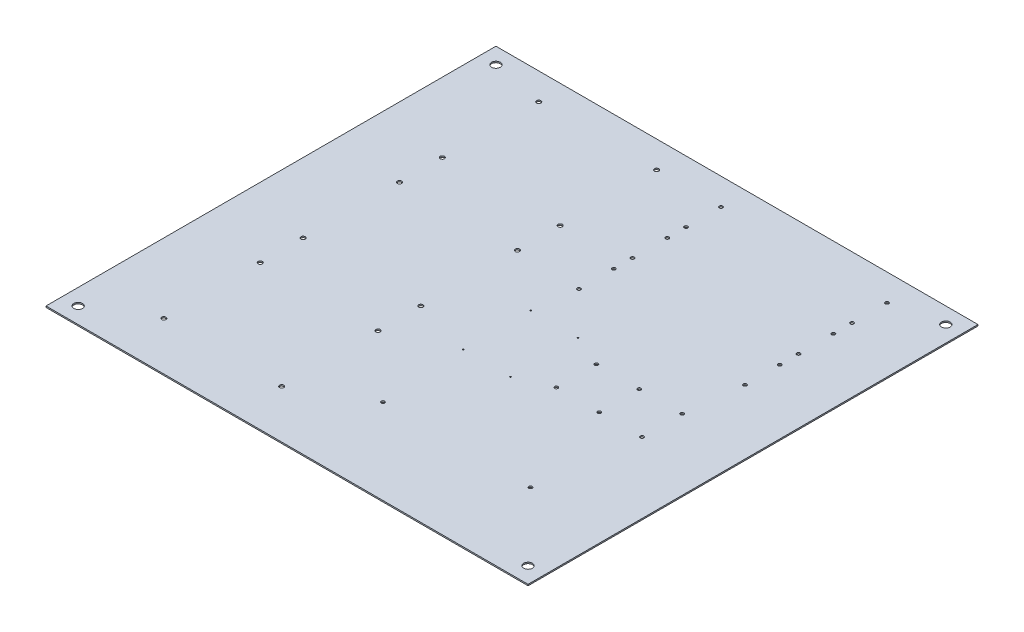
SolidWorks part; units mm, degrees
ref_plane "Front Plane" through (0, 0, 0) normal (0, 0, 1) x (1, 0, 0)
ref_plane "Top Plane" through (0, 0, 0) normal (0, 1, 0) x (1, 0, 0)
ref_plane "Right Plane" through (0, 0, 0) normal (1, 0, 0) x (0, 0, -1)
sketch "Sketch1" plane through (0, 0, 0) normal (0, 1, 0) x (1, 0, 0)
  line L1 (0, 0) -> (571.5, 0)
  line L2 (0, 0) -> (0, 533.4)
  line L3 (0, 533.4) -> (571.5, 533.4)
  line L4 (571.5, 0) -> (571.5, 533.4)
  dimension "D1" = 533.4
  dimension "D2" = 571.5
extrude "Boss-Extrude1" add sketch "Sketch1" along normal blind 1.5875
hole_wizard "#10-32 Tapped Hole1" positions "Sketch3" profile "Sketch2" tap size "#10-32" standard "ANSI Inch" end condition through all
sketch "Sketch3" plane through (0, 1.5875, 0) normal (0, 1, 0) x (1, 0, 0)
  line L0 (571.5, 533.4) -> (0, 533.4) construction
  line L1 (0, 533.4) -> (0, 0) construction
  point P0 (298.45, 501.65)
  point P2 (495.3, 501.65)
  point P4 (298.45, 460.375)
  point P6 (495.3, 460.375)
  point P21 (298.45, 438.15)
  point P22 (495.3, 438.15)
  point P23 (298.45, 396.875)
  point P24 (495.3, 396.875)
  point P25 (298.45, 374.65)
  point P26 (495.3, 374.65)
  point P27 (298.45, 333.375)
  point P28 (495.3, 333.375)
  dimension "D1" = 196.85
  dimension "D2" = 41.275
  dimension "D3" = 31.75
  dimension "D4" = 298.45
  dimension "D6" = 63.5
  dimension "D5" = 3
sketch "Sketch2" plane through (298.45, 1.5875, -501.65) normal (1, 0, 0) x (0, 0, 1)
  line L0 (0, 0) -> (0, 1.5875)
  line L1 (0, 1.5875) -> (2.0193, 1.5875)
  line L2 (2.0193, 1.5875) -> (2.0193, 0)
  line L5 (2.0193, 0) -> (0, 0)
  line L11 (0, -6.35) -> (0, 107.95) construction
  dimension "Thru Tap Drill Dia." = 4.0386
  dimension "Thru Tap Drill Depth" = 1.5875
cosmetic thread "Hole Thread1"
cosmetic thread "Hole Thread2"
cosmetic thread "Hole Thread3"
cosmetic thread "Hole Thread4"
cosmetic thread "Hole Thread17"
cosmetic thread "Hole Thread18"
cosmetic thread "Hole Thread19"
cosmetic thread "Hole Thread20"
cosmetic thread "Hole Thread21"
cosmetic thread "Hole Thread22"
cosmetic thread "Hole Thread23"
cosmetic thread "Hole Thread24"
hole_wizard "1/4-20 Tapped Hole1" positions "Sketch4" profile "Sketch5" tap size "1/4-20" standard "ANSI Inch" end condition through all
sketch "Sketch4" plane through (0, 1.5875, 0) normal (0, 1, 0) x (1, 0, 0)
  line L0 (571.5, 533.4) -> (0, 533.4) construction
  line L1 (0, 533.4) -> (0, 0) construction
  point P0 (82.55, 501.65)
  point P2 (82.55, 387.35)
  point P4 (222.25, 387.35)
  point P6 (222.25, 501.65)
  point P23 (82.55, 336.55)
  point P24 (82.55, 222.25)
  point P25 (222.25, 222.25)
  point P26 (222.25, 336.55)
  point P27 (82.55, 171.45)
  point P28 (82.55, 57.15)
  point P29 (222.25, 57.15)
  point P30 (222.25, 171.45)
  dimension "D1" = 114.3
  dimension "D2" = 139.7
  dimension "D3" = 31.75
  dimension "D4" = 82.55
  dimension "D6" = 50.8
  dimension "D5" = 3
sketch "Sketch5" plane through (82.55, 1.5875, -501.65) normal (1, 0, 0) x (0, 0, 1)
  line L0 (0, 0) -> (0, 1.5875)
  line L1 (0, 1.5875) -> (2.5527, 1.5875)
  line L2 (2.5527, 1.5875) -> (2.5527, 0)
  line L5 (2.5527, 0) -> (0, 0)
  line L11 (0, -6.35) -> (0, 107.95) construction
  dimension "Thru Tap Drill Dia." = 5.1054
  dimension "Thru Tap Drill Depth" = 1.5875
cosmetic thread "Hole Thread5"
cosmetic thread "Hole Thread6"
cosmetic thread "Hole Thread7"
cosmetic thread "Hole Thread8"
cosmetic thread "Hole Thread9"
cosmetic thread "Hole Thread10"
cosmetic thread "Hole Thread11"
cosmetic thread "Hole Thread12"
cosmetic thread "Hole Thread13"
cosmetic thread "Hole Thread14"
cosmetic thread "Hole Thread15"
cosmetic thread "Hole Thread16"
hole_wizard "M2x0.4 Tapped Hole1" positions "Sketch6" profile "Sketch7" tap size "M2x0.4" standard "ANSI Metric" end condition through all
sketch "Sketch6" plane through (0, 1.5875, 0) normal (0, 1, 0) x (1, 0, 0)
  line L0 (0, 533.4) -> (0, 0) construction
  circle A1 centre (298.45, 333.375) radius 2.0193 construction
  point P0 (292.1, 282.575)
  point P2 (348.1, 282.575)
  point P4 (292.1, 202.575)
  point P6 (348.1, 202.575)
  dimension "D1" = 80
  dimension "D2" = 56
  dimension "D3" = 292.1
  dimension "D4" = 50.8
sketch "Sketch7" plane through (292.1, 1.5875, -282.575) normal (1, 0, 0) x (0, 0, 1)
  line L0 (0, 0) -> (0, 1.5875)
  line L1 (0, 1.5875) -> (0.8, 1.5875)
  line L2 (0.8, 1.5875) -> (0.8, 0)
  line L5 (0.8, 0) -> (0, 0)
  line L11 (0, -6.35) -> (0, 107.95) construction
  dimension "Thru Tap Drill Dia." = 1.6
  dimension "Thru Tap Drill Depth" = 1.5875
cosmetic thread "Hole Thread25"
cosmetic thread "Hole Thread26"
cosmetic thread "Hole Thread27"
cosmetic thread "Hole Thread28"
hole_wizard "#10-32 Tapped Hole2" positions "Sketch8" profile "Sketch9" tap size "#10-32" standard "ANSI Inch" end condition through all
sketch "Sketch8" plane through (0, 1.5875, 0) normal (0, 1, 0) x (1, 0, 0)
  circle A4 centre (348.1, 282.575) radius 0.8 construction
  point P0 (386.2, 266.324)
  point P2 (386.2, 218.826)
  point P22 (437, 266.324)
  point P23 (437, 218.826)
  point P24 (487.8, 266.324)
  point P25 (487.8, 218.826)
  dimension "D2" = 16.251
  dimension "D3" = 38.1
  dimension "D1" = 47.498
  dimension "D5" = 50.8
  dimension "D4" = 3
sketch "Sketch9" plane through (386.2, 1.5875, -266.324) normal (1, 0, 0) x (0, 0, 1)
  line L0 (0, 0) -> (0, 1.5875)
  line L1 (0, 1.5875) -> (2.0193, 1.5875)
  line L2 (2.0193, 1.5875) -> (2.0193, 0)
  line L5 (2.0193, 0) -> (0, 0)
  line L11 (0, -6.35) -> (0, 107.95) construction
  dimension "Thru Tap Drill Dia." = 4.0386
  dimension "Thru Tap Drill Depth" = 1.5875
cosmetic thread "Hole Thread29"
cosmetic thread "Hole Thread30"
cosmetic thread "Hole Thread31"
cosmetic thread "Hole Thread32"
cosmetic thread "Hole Thread33"
cosmetic thread "Hole Thread34"
hole_wizard "#10-32 Tapped Hole3" positions "Sketch10" profile "Sketch11" tap size "#10-32" standard "ANSI Inch" end condition through all
sketch "Sketch10" plane through (0, 1.5875, 0) normal (0, 1, 0) x (1, 0, 0)
  line L0 (0, 533.4) -> (0, 0) construction
  circle A0 centre (348.1, 202.575) radius 0.8 construction
  point P0 (298.45, 100.975)
  point P2 (473.456, 100.975)
  dimension "D1" = 175.006
  dimension "D2" = 101.6
  dimension "D3" = 298.45
sketch "Sketch11" plane through (298.45, 1.5875, -100.975) normal (1, 0, 0) x (0, 0, 1)
  line L0 (0, 0) -> (0, 1.5875)
  line L1 (0, 1.5875) -> (2.0193, 1.5875)
  line L2 (2.0193, 1.5875) -> (2.0193, 0)
  line L5 (2.0193, 0) -> (0, 0)
  line L11 (0, -6.35) -> (0, 107.95) construction
  dimension "Thru Tap Drill Dia." = 4.0386
  dimension "Thru Tap Drill Depth" = 1.5875
cosmetic thread "Hole Thread35"
cosmetic thread "Hole Thread36"
hole_wizard "3/8 Clearance Hole1" positions "Sketch12" profile "Sketch13" hole size "3/8" standard "ANSI Inch" end condition through all
sketch "Sketch12" plane through (0, 1.5875, 0) normal (0, 1, 0) x (1, 0, 0)
  line L0 (0, 266.7) -> (-33.6931, 266.7)
  line L1 (0, 533.4) -> (0, 0) construction
  line L3 (285.75, 533.4) -> (285.75, 552.2627)
  line L4 (571.5, 533.4) -> (0, 533.4) construction
  point P0 (19.05, 514.35)
  point P14 (552.45, 514.35)
  point P15 (552.45, 19.05)
  point P16 (19.05, 19.05)
  dimension "D1" = 495.3
  dimension "D2" = 533.4
sketch "Sketch13" plane through (19.05, 1.5875, -514.35) normal (1, 0, 0) x (0, 0, 1)
  line L0 (0, 0) -> (0, 1.5875)
  line L1 (0, 1.5875) -> (5.1587, 1.5875)
  line L2 (5.1587, 1.5875) -> (5.1587, 0)
  line L5 (5.1587, 0) -> (0, 0)
  line L11 (0, -6.35) -> (0, 107.95) construction
  dimension "Thru Hole Dia." = 10.3175
  dimension "Thru Hole Depth" = 1.5875
